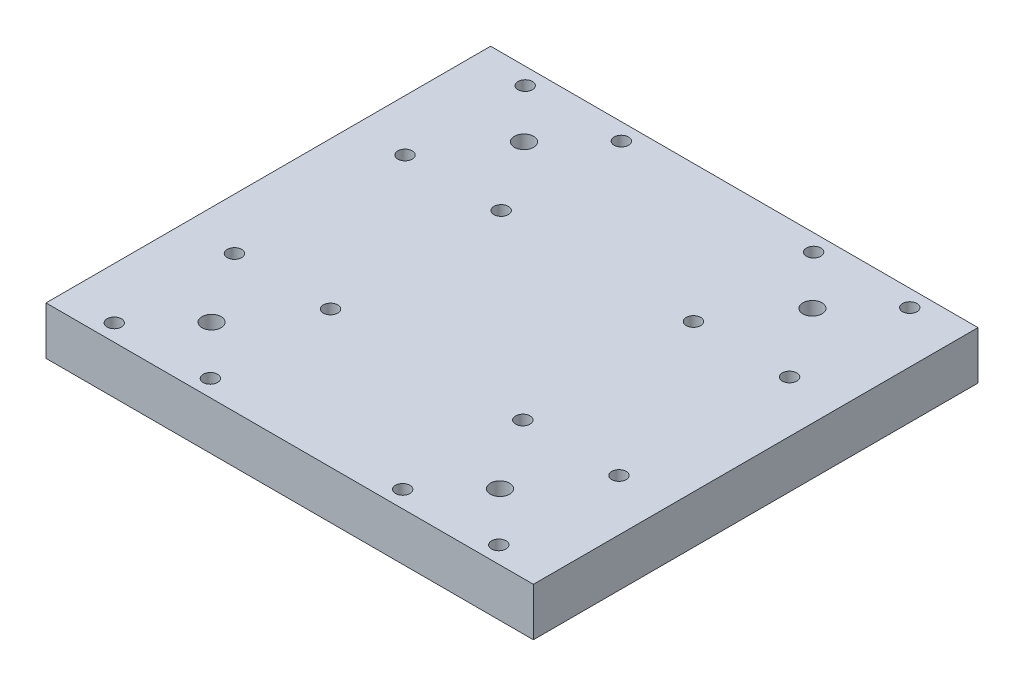
SolidWorks part; units mm, degrees
ref_plane "Front Plane" through (0, 0, 0) normal (0, 0, 1) x (1, 0, 0)
ref_plane "Top Plane" through (0, 0, 0) normal (0, 1, 0) x (1, 0, 0)
ref_plane "Right Plane" through (0, 0, 0) normal (1, 0, 0) x (0, 0, -1)
sketch "Sketch1" plane through (0, 0, 0) normal (0, 1, 0) x (1, 0, 0)
  line L0 (-55, 0) -> (55, 0) construction
  line L1 (-50.7, -46.25) -> (50.7, -46.25)
  line L2 (-50.7, -46.25) -> (-50.7, 46.25)
  line L3 (-50.7, 46.25) -> (50.7, 46.25)
  line L4 (50.7, -46.25) -> (50.7, 46.25)
  line L5 (-50.7, -46.25) -> (50.7, 46.25) construction
  line L6 (-50.7, 46.25) -> (50.7, -46.25) construction
  line L9 (0, -55) -> (0, 55) construction
  circle A0 centre (-40, 42.75) radius 1.5
  circle A1 centre (-20, 42.75) radius 1.5
  circle A2 centre (-20, 17.75) radius 1.5
  circle A3 centre (-40, 17.75) radius 1.5
  circle A16 centre (-40, -42.75) radius 1.5
  circle A17 centre (-20, -42.75) radius 1.5
  circle A18 centre (-20, -17.75) radius 1.5
  circle A19 centre (-40, -17.75) radius 1.5
  circle A20 centre (40, -17.75) radius 1.5
  circle A21 centre (20, -17.75) radius 1.5
  circle A22 centre (20, -42.75) radius 1.5
  circle A23 centre (40, -42.75) radius 1.5
  circle A24 centre (40, 17.75) radius 1.5
  circle A25 centre (20, 17.75) radius 1.5
  circle A26 centre (20, 42.75) radius 1.5
  circle A27 centre (40, 42.75) radius 1.5
  circle A28 centre (-30, 32.5) radius 2
  circle A29 centre (30, 32.5) radius 2
  circle A30 centre (30, -32.5) radius 2
  circle A31 centre (-30, -32.5) radius 2
  point P0 (0, 0)
  dimension "D3" = 2
  dimension "D5" = 3.5
  dimension "D6" = 10.7
  dimension "D7" = 25
  dimension "D8" = 20
  dimension "D9" = 3
  dimension "D10" = 32.5
  dimension "D11" = 30
  dimension "D12" = 4
  dimension "D1" = 92.5
  dimension "D2" = 101.4
  dimension "D4" = 2
extrude "Boss-Extrude1" add sketch "Sketch1" along normal blind 10
